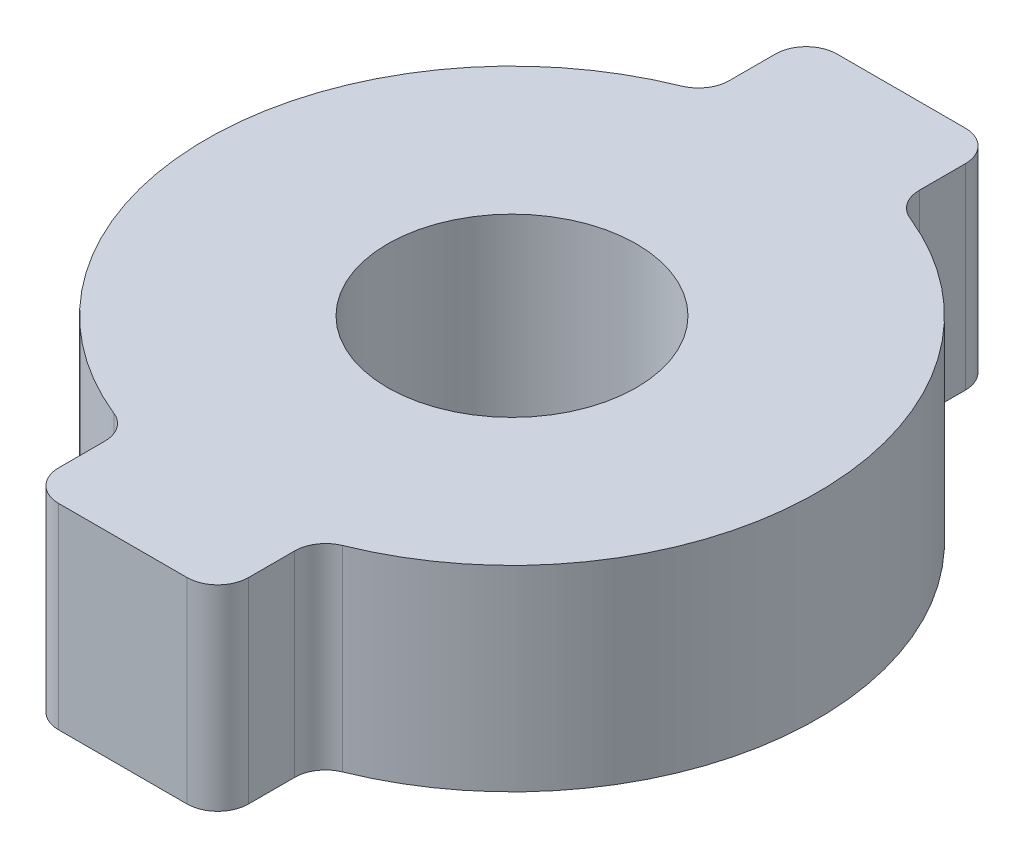
SolidWorks part; units mm, degrees
material "Balsa"
ref_plane "Front Plane" through (0, 0, 0) normal (0, 0, 1) x (1, 0, 0)
ref_plane "Top Plane" through (0, 0, 0) normal (0, 1, 0) x (1, 0, 0)
ref_plane "Right Plane" through (0, 0, 0) normal (1, 0, 0) x (0, 0, -1)
sketch "Sketch1" plane through (0, 0, 0) normal (0, 1, 0) x (1, 0, 0)
  circle A0 centre (0, 0) radius 9.9
  circle A1 centre (0, 0) radius 4.03
  dimension "D1" = 19.8
  dimension "D2" = 8.06
extrude "Boss-Extrude1" add sketch "Sketch1" along normal blind 6.35
other "Move Face1" [suppressed] parameters "D1"=0.08
sketch "Sketch2" plane through (0, 0, 0) normal (0, -1, 0) x (1, 0, 0)
  line L0 (-3.075, 9.4103) -> (3.075, 9.4103)
  line L1 (3.075, 9.4103) -> (3.075, 12.6)
  line L2 (3.075, 12.6) -> (-3.075, 12.6)
  line L3 (-3.075, 12.6) -> (-3.075, 9.4103)
  line L4 (0, 0) -> (0, 9.4103) construction
  line L5 (0, 0) -> (25.791, 0) construction
  line L6 (-3.075, -9.4103) -> (3.075, -9.4103)
  line L7 (3.075, -9.4103) -> (3.075, -12.6)
  line L8 (3.075, -12.6) -> (-3.075, -12.6)
  line L9 (-3.075, -12.6) -> (-3.075, -9.4103)
  circle A0 centre (0, 0) radius 9.9 construction
  dimension "D1" = 6.15
  dimension "D2" = 25.2
extrude "Boss-Extrude2" add sketch "Sketch2" against normal through all
fillet "Fillet2" radius 1 8 edges at (3.075, 3.175, -9.4103) (3.075, 3.175, -12.6) (-3.075, 3.175, -12.6) (-3.075, 3.175, -9.4103) (-3.075, 3.175, 9.4103) (-3.075, 3.175, 12.6) (3.075, 3.175, 12.6) (3.075, 3.175, 9.4103)
